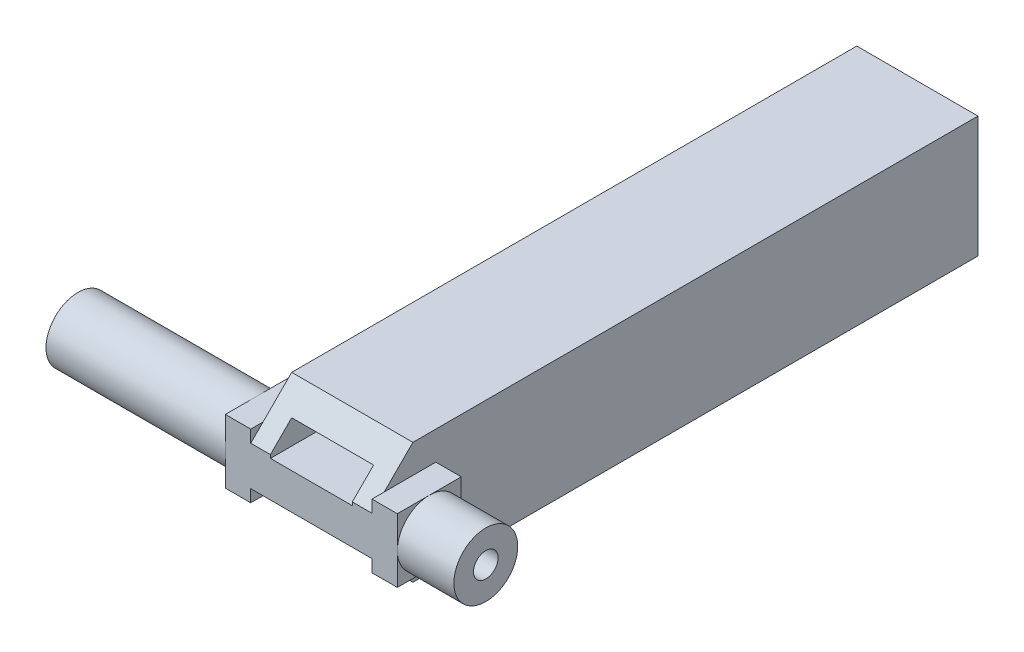
SolidWorks part; units mm, degrees
ref_plane "Спереди" through (0, 0, 0) normal (0, 0, 1) x (1, 0, 0)
ref_plane "Сверху" through (0, 0, 0) normal (0, 1, 0) x (1, 0, 0)
ref_plane "Справа" through (0, 0, 0) normal (1, 0, 0) x (0, 0, -1)
sketch "Эскиз1" plane through (0, 0, 0) normal (1, 0, 0) x (0, 0, -1)
  line L1 (37, -7.4) -> (-37, -7.4)
  line L2 (37, -7.4) -> (37, 7.4)
  line L3 (37, 7.4) -> (-37, 7.4)
  line L4 (-37, -7.4) -> (-37, 7.4)
  line L5 (37, -7.4) -> (-37, 7.4) construction
  line L6 (37, 7.4) -> (-37, -7.4) construction
  point P0 (0, 0)
  dimension "D1" = 14.8
  dimension "D2" = 74
extrude "Бобышка-Вытянуть1" add sketch "Эскиз1" along normal blind 14.8
sketch "Эскиз2" plane through (0, 0, -37) normal (0, 0, -1) x (-1, 0, 0)
  line L0 (0, 7.4) -> (-14.8, -7.4) construction
  line L2 (-2.4, -5) -> (-12.4, -5)
  line L3 (-2.4, -5) -> (-2.4, 5)
  line L4 (-2.4, 5) -> (-12.4, 5)
  line L5 (-12.4, -5) -> (-12.4, 5)
  line L6 (-2.4, -5) -> (-12.4, 5) construction
  line L7 (-2.4, 5) -> (-12.4, -5) construction
  point P4 (-7.4, 0)
  dimension "D1" = 10
extrude "Вырез-Вытянуть1" cut sketch "Эскиз2" against normal blind 65
sketch "Эскиз3" plane through (14.8, 0, 0) normal (1, 0, 0) x (0, 0, -1)
  line L0 (37, 0) -> (-37, 0) construction
  line L1 (37, -7.4) -> (37, 7.4) construction
  line L2 (-37, 7.4) -> (-37, -7.4) construction
  circle A0 centre (-33.1, 0) radius 3.9
  dimension "D1" = 7.8
extrude "Бобышка-Вытянуть2" add sketch "Эскиз3" along normal blind 10
sketch "Эскиз4" plane through (0, 0, 0) normal (-1, 0, 0) x (0, 0, 1)
  line L0 (37, 0) -> (-37, 0) construction
  line L1 (37, 7.4) -> (37, -7.4) construction
  line L2 (-37, -7.4) -> (-37, 7.4) construction
  circle A0 centre (33.1, 0) radius 3.9
  dimension "D1" = 7.8
extrude "Бобышка-Вытянуть3" add sketch "Эскиз4" along normal blind 25
chamfer "Фаска1" distance 5 angle 45 2 edges at (7.4, -7.4, 37) (7.4, 7.4, 37)
sketch "Эскиз5" plane through (-25, 0, 0) normal (-1, 0, 0) x (0, 0, 1)
  line L0 (33.1, 3.9) -> (33.1, -3.9) construction
  line L1 (31.6738, 3.6299) -> (33.1, 0) construction
  line L2 (30.0118, 2.1173) -> (33.9209, 3.6532)
  line L3 (33.9209, 3.6532) -> (36.1882, -2.1173)
  line L4 (36.1882, -2.1173) -> (32.2791, -3.6532)
  line L5 (32.2791, -3.6532) -> (30.0118, 2.1173)
  line L6 (30.0118, 2.1173) -> (36.1882, -2.1173) construction
  circle A0 centre (33.1, 0) radius 3.9 construction
  point P9 (33.1, 0)
  dimension "D1" = 21.45
  dimension "D2" = 4.2
  dimension "D3" = 6.2
extrude "Вырез-Вытянуть2" cut sketch "Эскиз5" against normal blind 6
sketch "Эскиз8" plane through (24.8, 0, 0) normal (1, 0, 0) x (0, 0, -1)
  circle A0 centre (-33.1, 0) radius 1.5
  dimension "D1" = 3
extrude "Вырез-Вытянуть4" cut sketch "Эскиз8" against normal through all
sketch "Эскиз9" plane through (0, 0, 0) normal (-1, 0, 0) x (0, 0, 1)
  line L1 (37, -3.9) -> (29.2, -3.9)
  line L2 (37, -3.9) -> (37, 3.9)
  line L3 (37, 3.9) -> (29.2, 3.9)
  line L4 (29.2, -3.9) -> (29.2, 3.9)
  line L5 (37, -3.9) -> (29.2, 3.9) construction
  line L6 (37, 3.9) -> (29.2, -3.9) construction
  circle A0 centre (33.1, 0) radius 3.9 construction
  circle A1 centre (33.1, 0) radius 1.5
  point P0 (33.1, 0)
  point P6 (29.2, 0)
  point P11 (33.1, 3.9)
  dimension "D1" = 3
extrude "Бобышка-Вытянуть4" add sketch "Эскиз9" along normal blind 3.1
sketch "Эскиз10" plane through (14.8, 0, 0) normal (1, 0, 0) x (0, 0, -1)
  line L1 (-37, -3.9) -> (-29.2, -3.9)
  line L2 (-37, -3.9) -> (-37, 3.9)
  line L3 (-37, 3.9) -> (-29.2, 3.9)
  line L4 (-29.2, -3.9) -> (-29.2, 3.9)
  line L5 (-37, -3.9) -> (-29.2, 3.9) construction
  line L6 (-37, 3.9) -> (-29.2, -3.9) construction
  circle A0 centre (-33.1, 0) radius 3.9 construction
  point P0 (-33.1, 0)
  point P6 (-29.2, 0)
  point P9 (-33.1, 3.9)
extrude "Бобышка-Вытянуть5" add sketch "Эскиз10" along normal blind 3.1
sketch "Эскиз11" plane through (0, 0, 28) normal (0, 0, -1) x (-1, 0, 0)
  line L0 (-12.4, 3.5) -> (-2.4, 3.5) construction
  line L1 (-12.4, 5) -> (-12.4, -5) construction
  line L2 (-2.4, -5) -> (-2.4, 5) construction
  line L4 (-2.4, 2) -> (-12.4, 2)
  line L5 (-2.4, 2) -> (-2.4, 5)
  line L6 (-2.4, 5) -> (-12.4, 5)
  line L7 (-12.4, 2) -> (-12.4, 5)
  line L8 (-2.4, 2) -> (-12.4, 5) construction
  line L9 (-2.4, 5) -> (-12.4, 2) construction
  point P6 (-7.4, 3.5)
  dimension "D1" = 1.5
extrude "Вырез-Вытянуть5" cut sketch "Эскиз11" against normal through all
